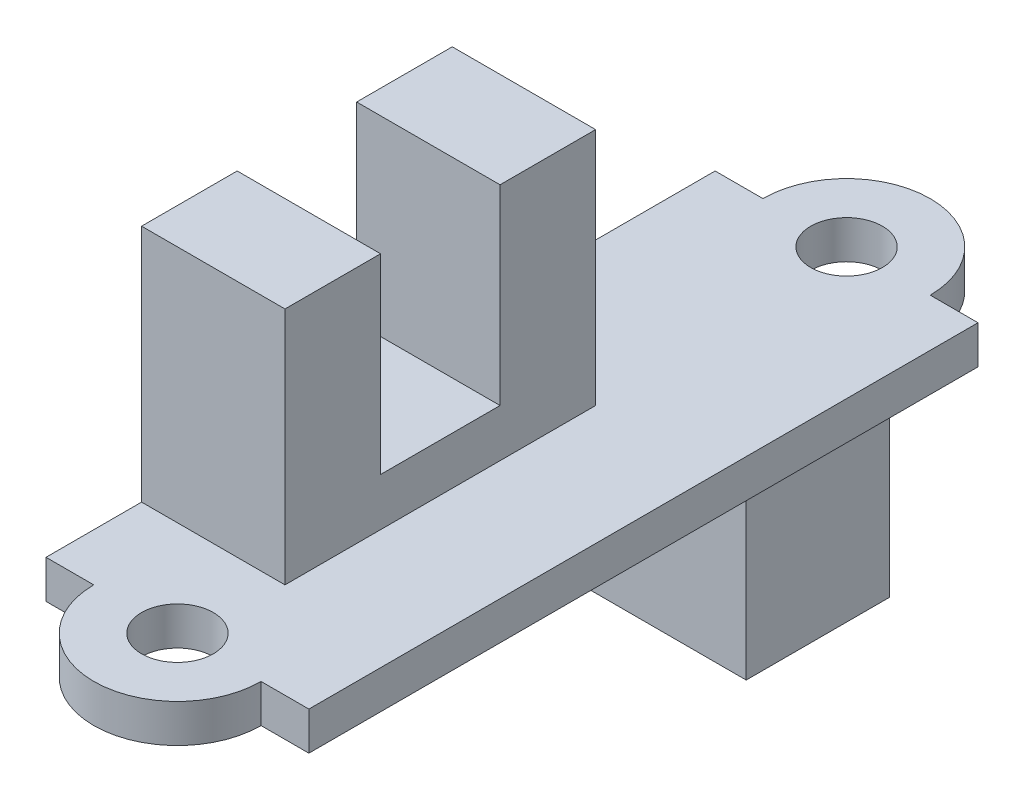
SolidWorks part; units mm, degrees
ref_plane "Front Plane" through (0, 0, 0) normal (0, 0, 1) x (1, 0, 0)
ref_plane "Top Plane" through (0, 0, 0) normal (0, 1, 0) x (1, 0, 0)
ref_plane "Right Plane" through (0, 0, 0) normal (1, 0, 0) x (0, 0, -1)
sketch "Sketch1" plane through (0, 0, 0) normal (0, 1, 0) x (1, 0, 0)
  line L1 (-5.5, 28) -> (-3.5, 28)
  line L2 (-5.5, 28) -> (-5.5, 0)
  line L3 (-5.5, 0) -> (-3.5, 0)
  line L4 (5.5, 28) -> (5.5, 0)
  line L5 (3.5, 28) -> (5.5, 28)
  line L6 (3.5, 0) -> (5.5, 0)
  circle A0 centre (0, 0) radius 1.5
  circle A1 centre (0, 28) radius 1.5
  arc A2 (3.5, 28) -> (-3.5, 28) centre (0, 28) ccw
  arc A3 (-3.5, 0) -> (3.5, 0) centre (0, 0) ccw
  point P6 (0, 0)
  point P11 (5.4984, -1.2946)
  point P12 (0, 0)
  point P13 (0, 0)
  point P17 (0, 0)
  point P18 (-2.9568, 28)
  dimension "D1" = 3
  dimension "D2" = 7
  dimension "D3" = 3
  dimension "D4" = 7
  dimension "D5" = 28
  dimension "D6" = 11
extrude "Boss-Extrude1" add sketch "Sketch1" along normal blind 1.6
sketch "Sketch3" plane through (5.5, 0, 0) normal (1, 0, 0) x (0, 0, -1)
  line L0 (4, 1.6) -> (4, 11.6)
  line L1 (4, 11.6) -> (8, 11.6)
  line L2 (8, 11.6) -> (8, 3.6)
  line L3 (8, 3.6) -> (13, 3.6)
  line L4 (13, 3.6) -> (13, 11.6)
  line L5 (13, 11.6) -> (17, 11.6)
  line L6 (17, 11.6) -> (17, 1.6)
  line L7 (17, 1.6) -> (4, 1.6)
  dimension "D1" = 13
  dimension "D2" = 10
  dimension "D3" = 5
  dimension "D4" = 2
  dimension "D5" = 4
  dimension "D6" = 1.6
extrude "Boss-Extrude2" add sketch "Sketch3" along normal blind 6 from offset 11 offset against normal yes
sketch "Sketch5" plane through (0, 0, 0) normal (0, -1, 0) x (1, 0, 0)
  line L0 (-5.5, -28) -> (-5.5, 0) construction
  line L1 (-5, -18.8) -> (5, -18.8)
  line L2 (-5, -18.8) -> (-5, -24.8)
  line L3 (-5, -24.8) -> (5, -24.8)
  line L4 (5, -18.8) -> (5, -24.8)
  line L5 (-3.5, -28) -> (-5.5, -28) construction
  dimension "D1" = 10
  dimension "D2" = 6
  dimension "D3" = 3.2
  dimension "D4" = 0.5
extrude "Boss-Extrude3" add sketch "Sketch5" along normal blind 7
